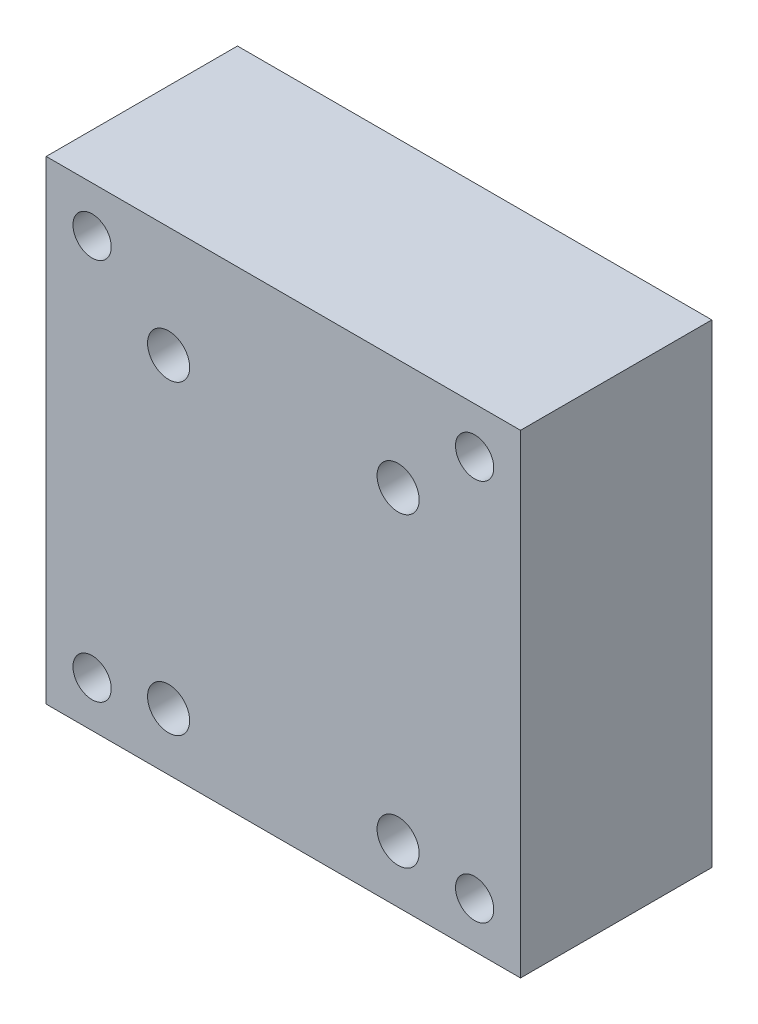
SolidWorks part; units mm, degrees
ref_plane "前视基准面" through (0, 0, 0) normal (0, 0, 1) x (1, 0, 0)
ref_plane "上视基准面" through (0, 0, 0) normal (0, 1, 0) x (1, 0, 0)
ref_plane "右视基准面" through (0, 0, 0) normal (1, 0, 0) x (0, 0, -1)
sketch "草图1" plane through (0, 0, 0) normal (0, 0, 1) x (1, 0, 0)
  line L1 (-31, 31) -> (31, 31)
  line L2 (-31, 31) -> (-31, -31)
  line L3 (-31, -31) -> (31, -31)
  line L4 (31, 31) -> (31, -31)
  line L5 (-31, 31) -> (31, -31) construction
  line L6 (-31, -31) -> (31, 31) construction
  point P0 (0, 0)
  dimension "D1" = 62
extrude "凸台-拉伸1" add sketch "草图1" along normal blind 25
sketch "草图2" plane through (0, 0, 0) normal (0, 0, -1) x (-1, 0, 0)
  line L1 (-25, 25) -> (25, 25) construction
  line L2 (-25, 25) -> (-25, -25) construction
  line L3 (-25, -25) -> (25, -25) construction
  line L4 (25, 25) -> (25, -25) construction
  line L5 (-25, 25) -> (25, -25) construction
  line L6 (-25, -25) -> (25, 25) construction
  point P0 (0, 0)
  dimension "D1" = 50
hole_wizard "M6 螺纹孔1" positions "3D草图1" profile "草图3" tap size "M6" standard "ISO" end condition through all
sketch3d "3D草图1"
  point P0 (25, 25, 0)
  point P3 (-25, 25, 0)
  point P6 (25, -25, 0)
  point P9 (-25, -25, 0)
sketch "草图3" plane through (25, 25, 0) normal (1, 0, 0) x (0, 1, 0)
  line L0 (0, 0) -> (0, 25)
  line L1 (0, 25) -> (2.5, 25)
  line L2 (2.5, 25) -> (2.5, 0)
  line L5 (2.5, 0) -> (0, 0)
  line L11 (0, -6.35) -> (0, 107.95) construction
  dimension "通孔螺纹孔钻头直径" = 5
  dimension "通孔螺纹孔钻头深度" = 25
cosmetic thread "孔螺蚊线1" parameters "D2"=6
cosmetic thread "孔螺蚊线2" parameters "D2"=6
cosmetic thread "孔螺蚊线3" parameters "D2"=6
cosmetic thread "孔螺蚊线4" parameters "D2"=6
sketch "草图4" plane through (0, 0, 0) normal (0, 0, -1) x (-1, 0, 0)
  line L0 (0, 0) -> (0, -3.5) construction
  line L1 (-15, 16.5) -> (15, 16.5) construction
  line L2 (-15, 16.5) -> (-15, -23.5) construction
  line L3 (-15, -23.5) -> (15, -23.5) construction
  line L4 (15, 16.5) -> (15, -23.5) construction
  line L5 (-15, 16.5) -> (15, -23.5) construction
  line L6 (-15, -23.5) -> (15, 16.5) construction
  line L7 (-25, -25) -> (25, -25) construction
  point P0 (0, -3.5)
  dimension "D1" = 40
  dimension "D2" = 30
  dimension "D3" = 1.5
hole_wizard "M5 六角凹头螺钉的柱形沉头孔1" positions "3D草图2" profile "草图5" counterbore size "M5" standard "ISO" end condition through all
sketch3d "3D草图2"
  point P0 (15, 16.5, 0)
  point P3 (-15, 16.5, 0)
  point P6 (-15, -23.5, 0)
  point P9 (15, -23.5, 0)
sketch "草图5" plane through (15, 16.5, 0) normal (1, 0, 0) x (0, 1, 0)
  line L0 (0, 0) -> (0, 25)
  line L1 (0, 25) -> (2.75, 25)
  line L3 (2.75, 25) -> (2.75, 20)
  line L4 (2.75, 20) -> (5, 20)
  line L5 (5, 20) -> (5, 0)
  line L7 (5, 0) -> (0, 0)
  line L11 (0, -6.35) -> (0, 107.95) construction
  dimension "通孔孔直径" = 5.5
  dimension "通孔孔深度" = 25
  dimension "柱形沉头孔直径" = 10
  dimension "柱形沉头孔深度" = 20
